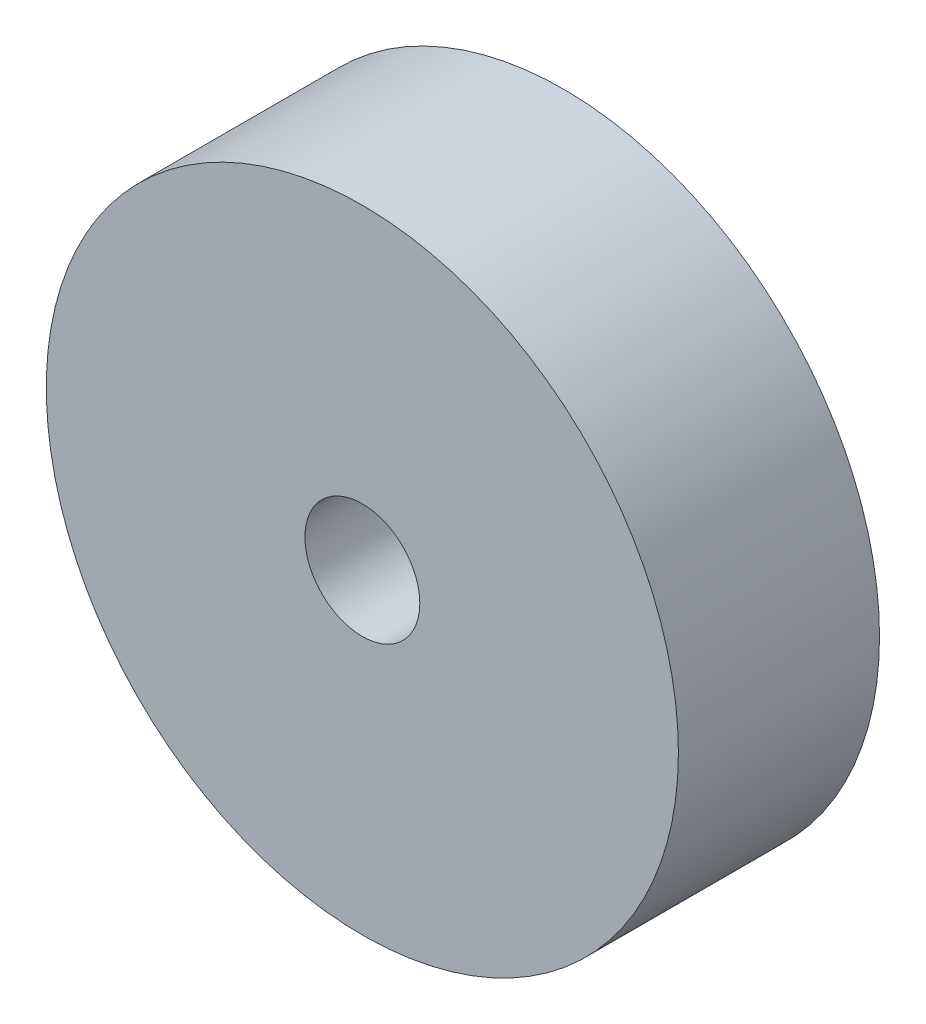
SolidWorks part; units mm, degrees
ref_plane "Front Plane" through (0, 0, 0) normal (0, 0, 1) x (1, 0, 0)
ref_plane "Top Plane" through (0, 0, 0) normal (0, 1, 0) x (1, 0, 0)
ref_plane "Right Plane" through (0, 0, 0) normal (1, 0, 0) x (0, 0, -1)
sketch "Sketch1" plane through (0, 0, 0) normal (0, 0, 1) x (1, 0, 0)
  circle A0 centre (0, 0) radius 11
  circle A1 centre (0, 0) radius 2
  dimension "D1" = 22
  dimension "D2" = 4
extrude "Boss-Extrude1" add sketch "Sketch1" along normal blind 7
